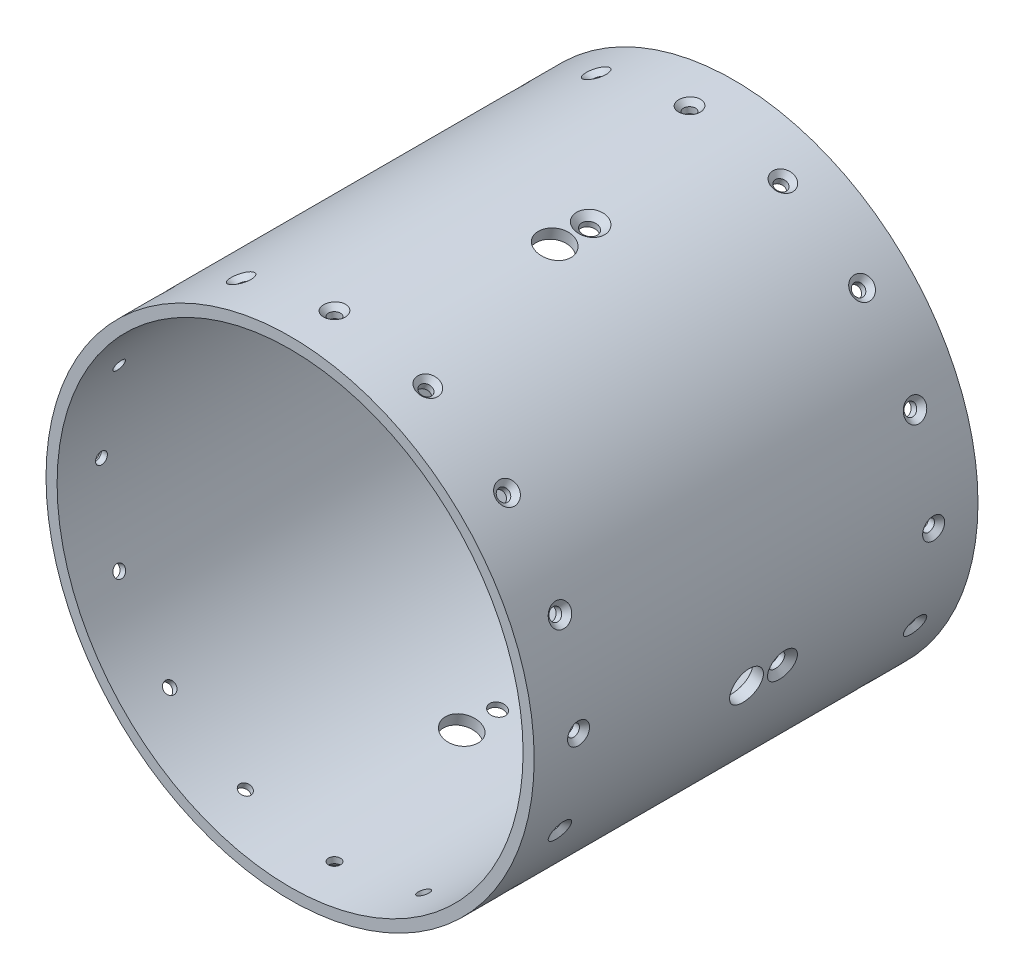
SolidWorks part; units mm, degrees
ref_plane "Front Plane" through (0, 0, 0) normal (0, 0, 1) x (1, 0, 0)
ref_plane "Top Plane" through (0, 0, 0) normal (0, 1, 0) x (1, 0, 0)
ref_plane "Right Plane" through (0, 0, 0) normal (1, 0, 0) x (0, 0, -1)
sketch "Sketch1" plane through (0, 0, 0) normal (0, 0, 1) x (1, 0, 0)
  circle A0 centre (0, 0) radius 66.675
  circle A1 centre (0, 0) radius 69.85
extrude "Extrude1" add sketch "Sketch1" along normal blind 127
sketch "Sketch4" plane through (0, 0, 0) normal (0, 0, -1) x (-1, 0, 0)
  circle A0 centre (0, 0) radius 66.675
sketch "Sketch5" plane through (0, 0, 127) normal (0, 0, 1) x (1, 0, 0)
  circle A0 centre (0, 0) radius 66.675
ref_plane "Plane1" through (0, 0, 12.7) normal (0, 0, 1) x (1, 0, 0)
ref_plane "Plane3" through (0, 0, 114.3) normal (0, 0, 1) x (1, 0, 0)
sketch "Sketch11" plane through (0, 0, 114.3) normal (0, 0, 1) x (1, 0, 0)
  line L0 (0, 0) -> (69.85, 0) construction
  circle A0 centre (0, 0) radius 69.85 construction
ref_plane "Plane4" through (69.85, 0, 114.3) normal (1, 0, 0) x (0, 0, -1)
hole_wizard "CSK for M3 Flat Head Machine Screw2" positions "Sketch13" profile "Sketch12" countersink size "M3" standard "Ansi Metric"
sketch "Sketch13" plane through (69.85, 0, 114.3) normal (1, 0, 0) x (0, 0, -1)
  point P1 (0, 0)
sketch "Sketch12" plane through (69.85, 0, 114.3) normal (0, 1, 0) x (0, 0, -1)
  line L0 (0, 0) -> (0, 13.2135)
  line L1 (0, 13.2135) -> (1.7, 12.192)
  line L2 (1.7, 12.192) -> (1.7, 1.45)
  line L3 (1.7, 1.45) -> (3.15, 0)
  line L5 (3.15, 0) -> (0, 0)
  line L6 (-1.7, 1.45) -> (-3.15, 0) construction
  line L10 (0, 13.2135) -> (-1.7, 12.192) construction
  line L11 (0, -6.35) -> (0, 107.95) construction
  dimension "Hole Dia." = 3.4
  dimension "Hole Depth" = 12.192
  dimension "Near C'Sink Dia." = 6.3
  dimension "Near C'Sink Angle" = 90
  dimension "Drill Angle" = 118
sketch "Sketch23" plane through (0, 0, 12.7) normal (0, 0, 1) x (1, 0, 0)
  line L0 (0, 0) -> (69.85, 0) construction
ref_plane "Plane7" through (69.85, 0, 12.7) normal (1, 0, 0) x (0, 0, -1)
hole_wizard "CSK for M3 Flat Head Machine Screw1" positions "Sketch29" profile "Sketch30" countersink size "M3" standard "Ansi Metric"
sketch "Sketch29" plane through (69.85, 0, 12.7) normal (1, 0, 0) x (0, 0, -1)
  point P1 (0, 0)
sketch "Sketch30" plane through (69.85, 0, 12.7) normal (0, 1, 0) x (0, 0, -1)
  line L0 (0, 0) -> (0, 13.2135)
  line L1 (0, 13.2135) -> (1.7, 12.192)
  line L2 (1.7, 12.192) -> (1.7, 1.45)
  line L3 (1.7, 1.45) -> (3.15, 0)
  line L5 (3.15, 0) -> (0, 0)
  line L6 (-1.7, 1.45) -> (-3.15, 0) construction
  line L10 (0, 13.2135) -> (-1.7, 12.192) construction
  line L11 (0, -6.35) -> (0, 107.95) construction
  dimension "Hole Dia." = 3.4
  dimension "Hole Depth" = 12.192
  dimension "Near C'Sink Dia." = 6.3
  dimension "Near C'Sink Angle" = 90
  dimension "Drill Angle" = 118
pattern_circular "CirPattern1" count 16 over 360 about axis through (0, 0, 127) along (0, 0, -1) of "CSK for M3 Flat Head Machine Screw2", "CSK for M3 Flat Head Machine Screw1"
ref_plane "Plane8" through (0, 0, 64.77) normal (0, 0, 1) x (1, 0, 0)
sketch "Sketch35" plane through (0, 0, 64.77) normal (0, 0, 1) x (1, 0, 0)
  line L0 (69.8153, 0) -> (68.4, 0) construction
  arc A0 (69.85, 0) -> (68.5079, -13.6271) centre (0, 0) cw
  circle A1 centre (0, 0) radius 69.85 construction
sketch "Sketch31" plane through (0, 0, 64.77) normal (0, 0, 1) x (1, 0, 0)
  line L0 (0, 0) -> (68.5079, -13.6271) construction
ref_plane "Plane6" through (68.5079, -13.6271, 64.77) normal (0.9808, -0.1951, 0) x (0.1951, 0.9808, 0)
sketch "Sketch15" plane through (68.5079, -13.6271, 64.77) normal (0.9808, -0.1951, 0) x (0.1951, 0.9808, 0)
  line L0 (0, 0.1207) -> (0, -10.16) construction
hole_wizard "3/8 (0.375) Diameter Hole1" positions "Sketch33" profile "Sketch32" hole size "3/8" standard "Ansi Inch"
sketch "Sketch33" plane through (68.5079, -13.6271, 64.77) normal (0.9808, -0.1951, 0) x (0.1951, 0.9808, 0)
  point P1 (0, 0.1207)
sketch "Sketch32" plane through (68.5079, -13.6271, 64.8907) normal (0, 0, 1) x (0.1951, 0.9808, 0)
  line L0 (0, 0) -> (0, 15.5616)
  line L1 (0, 15.5616) -> (4.7625, 12.7)
  line L2 (4.7625, 12.7) -> (4.7625, 0)
  line L5 (4.7625, 0) -> (0, 0)
  line L10 (0, 15.5616) -> (-4.7625, 12.7) construction
  line L11 (0, -6.35) -> (0, 107.95) construction
  dimension "Hole Dia." = 9.525
  dimension "Hole Depth" = 12.7
  dimension "Drill Angle" = 118
hole_wizard "CSK for #8 Flat Head Machine Screw (100)2" positions "Sketch21" profile "Sketch22" countersink size "#8" standard "Ansi Inch"
sketch "Sketch21" plane through (68.5079, -13.6271, 64.77) normal (0.9808, -0.1951, 0) x (0.1951, 0.9808, 0)
  point P1 (0, -10.16)
sketch "Sketch22" plane through (68.5079, -13.6271, 54.61) normal (0, 0, 1) x (0.1951, 0.9808, 0)
  line L0 (0, 0) -> (0, 13.5427)
  line L1 (0, 13.5427) -> (2.2479, 12.192)
  line L2 (2.2479, 12.192) -> (2.2479, 1.6518)
  line L3 (2.2479, 1.6518) -> (4.2164, 0)
  line L5 (4.2164, 0) -> (0, 0)
  line L6 (-2.2479, 1.6518) -> (-4.2164, 0) construction
  line L10 (0, 13.5427) -> (-2.2479, 12.192) construction
  line L11 (0, -6.35) -> (0, 107.95) construction
  dimension "Hole Dia." = 4.4958
  dimension "Hole Depth" = 12.192
  dimension "Near C'Sink Dia." = 8.4328
  dimension "Near C'Sink Angle" = 100
  dimension "Drill Angle" = 118
pattern_circular "CirPattern2" count 4 over 360 about axis through (0, 0, 127) along (0, 0, -1) of "CSK for #8 Flat Head Machine Screw (100)2", "3/8 (0.375) Diameter Hole1"
ref_plane "Plane9" through (0, 0, 38.1) normal (0, 0, 1) x (1, 0, 0)
sketch "Sketch36" plane through (0, 0, 38.1) normal (0, 0, 1) x (1, 0, 0)
  line L0 (0, 0) -> (38.8066, -58.0782) construction
  line L4 (0, 0) -> (68.5079, -13.6271) construction
  circle A1 centre (0, 0) radius 69.85 construction
  dimension "D1" = 45
ref_plane "Plane10" through (38.8066, -58.0782, 38.1) normal (0.5556, -0.8315, 0) x (0.8315, 0.5556, 0)
hole_wizard "7/16 (0.4375) Diameter Hole1" positions "Sketch38" profile "Sketch39" hole size "7/16" standard "Ansi Inch"
sketch "Sketch38" plane through (38.8066, -58.0782, 38.1) normal (0.5556, -0.8315, 0) x (0.8315, 0.5556, 0)
  point P1 (0, 0)
sketch "Sketch39" plane through (38.8066, -58.0782, 38.1) normal (0, 0, 1) x (0.8315, 0.5556, 0)
  line L0 (0, 0) -> (0, 12.9905)
  line L1 (0, 12.9905) -> (5.5562, 9.652)
  line L2 (5.5562, 9.652) -> (5.5562, 0)
  line L5 (5.5562, 0) -> (0, 0)
  line L10 (0, 12.9905) -> (-5.5563, 9.652) construction
  line L11 (0, -6.35) -> (0, 107.95) construction
  dimension "Hole Dia." = 11.1125
  dimension "Hole Depth" = 9.652
  dimension "Drill Angle" = 118
